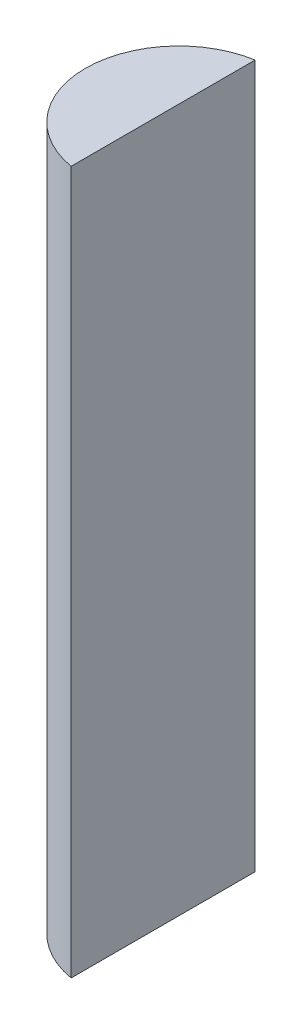
SolidWorks part; units mm, degrees
ref_plane "Front Plane" through (0, 0, 0) normal (0, 0, 1) x (1, 0, 0)
ref_plane "Top Plane" through (0, 0, 0) normal (0, 1, 0) x (1, 0, 0)
ref_plane "Right Plane" through (0, 0, 0) normal (1, 0, 0) x (0, 0, -1)
sketch "Sketch1" plane through (0, 0, 0) normal (0, 1, 0) x (1, 0, 0)
  line L0 (-2, -11.7814) -> (-2, 11.7814)
  arc A0 (-2, 11.7814) -> (-2, -11.7814) centre (0, 0) ccw
  dimension "D1" = 23.9
extrude "Boss-Extrude1" add sketch "Sketch1" along normal blind 90
